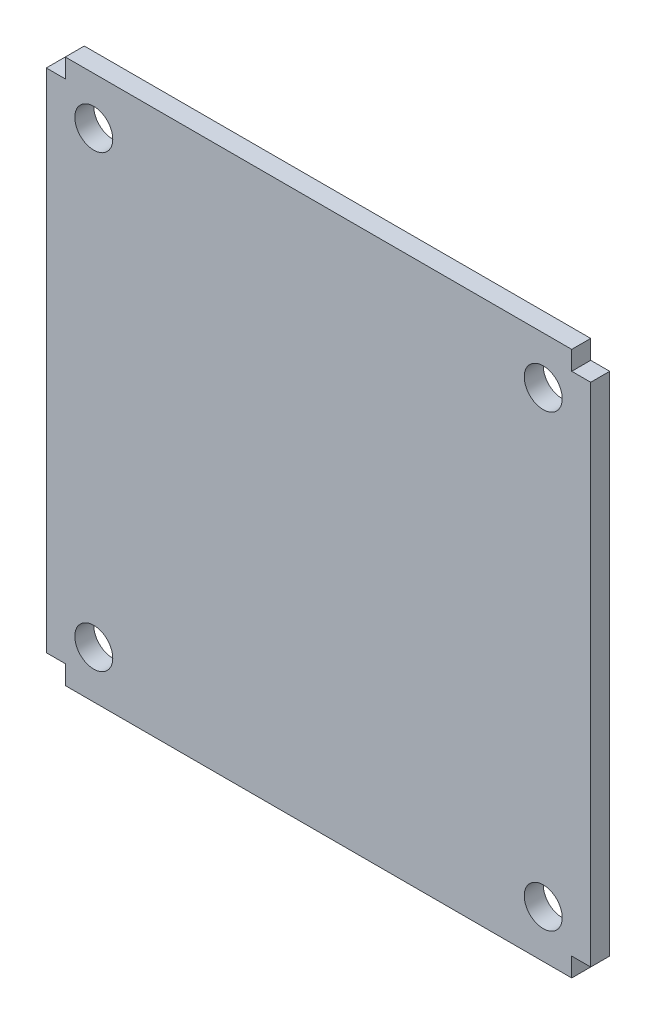
SolidWorks part; units mm, degrees
material "7075-T6, Plate (SS)"
ref_plane "Front Plane" through (0, 0, 0) normal (0, 0, 1) x (1, 0, 0)
ref_plane "Top Plane" through (0, 0, 0) normal (0, 1, 0) x (1, 0, 0)
ref_plane "Right Plane" through (0, 0, 0) normal (1, 0, 0) x (0, 0, -1)
sketch "Sketch1" plane through (0, 0, 0) normal (0, 0, 1) x (1, 0, 0)
  line L0 (-10.6381, 32.9766) -> (-10.6381, 29.9766)
  line L1 (-10.6381, 29.9766) -> (-13.6381, 29.9766)
  line L2 (-13.6381, 29.9766) -> (-13.6381, -50.0234)
  line L3 (-13.6381, -50.0234) -> (-10.6381, -50.0234)
  line L4 (-10.6381, -50.0234) -> (-10.6381, -53.0234)
  line L5 (-10.6381, -53.0234) -> (69.3619, -53.0234)
  line L6 (69.3619, -53.0234) -> (69.3619, -50.0234)
  line L7 (69.3619, -50.0234) -> (72.3619, -50.0234)
  line L8 (72.3619, -50.0234) -> (72.3619, 29.9766)
  line L9 (72.3619, 29.9766) -> (69.3619, 29.9766)
  line L10 (69.3619, 29.9766) -> (69.3619, 32.9766)
  line L11 (69.3619, 32.9766) -> (-10.6381, 32.9766)
  circle A0 centre (-6.1381, 25.4766) radius 3
  circle A1 centre (64.8619, 25.4766) radius 3
  circle A2 centre (-6.1381, -45.5234) radius 3
  circle A3 centre (64.8619, -45.5234) radius 3
  dimension "D19" = 6
  dimension "D20" = 6
  dimension "D21" = 6
  dimension "D22" = 6
  dimension "D1" = 3
  dimension "D2" = 3
  dimension "D3" = 80
  dimension "D4" = 3
  dimension "D5" = 3
  dimension "D6" = 80
  dimension "D7" = 3
  dimension "D8" = 3
  dimension "D9" = 80
  dimension "D10" = 3
  dimension "D11" = 71
  dimension "D12" = 71
  dimension "D13" = 4.5
  dimension "D14" = 71
  dimension "D15" = 71
  dimension "D16" = 4.5
  dimension "D17" = 4.5
  dimension "D18" = 4.5
extrude "Boss-Extrude1" add sketch "Sketch1" along normal blind 3
